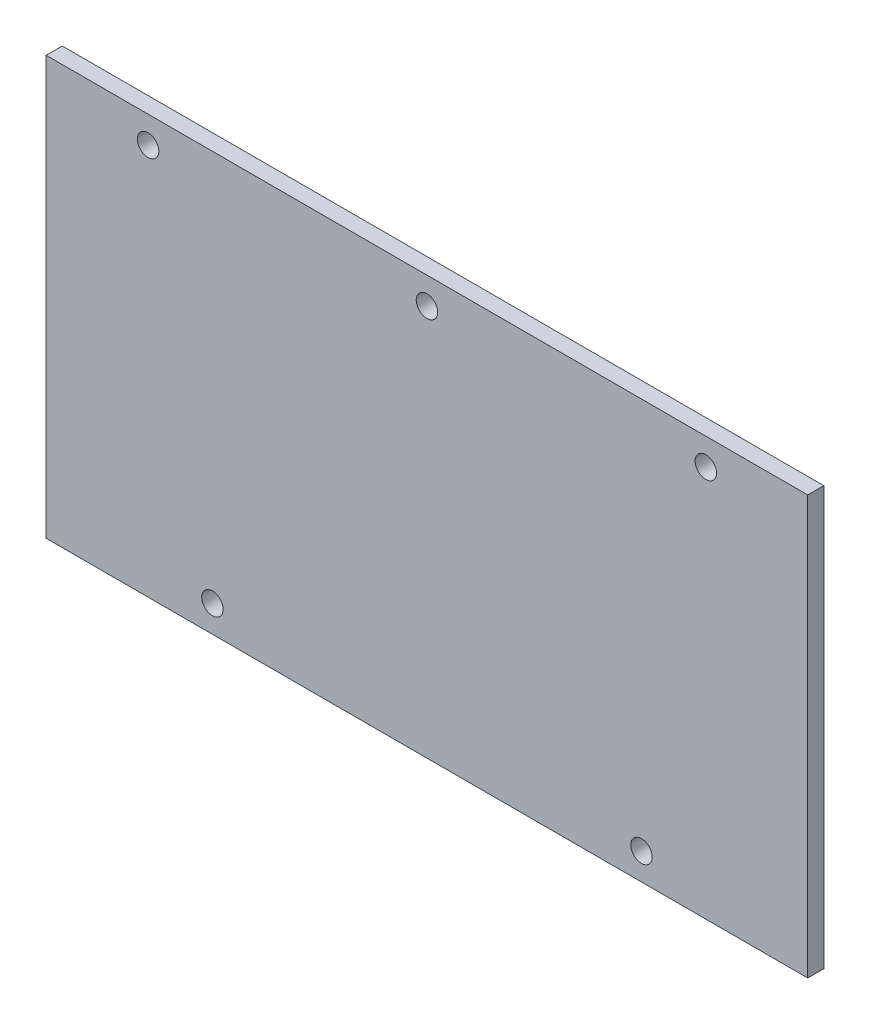
SolidWorks part; units mm, degrees
ref_plane "Спереди" through (0, 0, 0) normal (0, 0, 1) x (1, 0, 0)
ref_plane "Сверху" through (0, 0, 0) normal (0, 1, 0) x (1, 0, 0)
ref_plane "Справа" through (0, 0, 0) normal (1, 0, 0) x (0, 0, -1)
sketch "Эскиз1" plane through (0, 0, 0) normal (0, 0, 1) x (1, 0, 0)
  line L1 (35.5, 19.5) -> (-35.5, 19.5)
  line L2 (35.5, 19.5) -> (35.5, -19.5)
  line L3 (35.5, -19.5) -> (-35.5, -19.5)
  line L4 (-35.5, 19.5) -> (-35.5, -19.5)
  line L5 (35.5, 19.5) -> (-35.5, -19.5) construction
  line L6 (35.5, -19.5) -> (-35.5, 19.5) construction
  point P0 (0, 0)
  dimension "D1" = 39
  dimension "D2" = 71
extrude "Бобышка-Вытянуть1" add sketch "Эскиз1" along normal blind 1.5
sketch "Эскиз2" plane through (0, 0, 1.5) normal (0, 0, 1) x (1, 0, 0)
  line L1 (26, 17) -> (-26, 17) construction
  line L2 (26, 17) -> (26, -17) construction
  line L3 (26, -17) -> (-26, -17) construction
  line L4 (-26, 17) -> (-26, -17) construction
  line L5 (26, 17) -> (-26, -17) construction
  line L6 (26, -17) -> (-26, 17) construction
  circle A0 centre (26, 17) radius 1
  circle A1 centre (-26, 17) radius 1
  circle A2 centre (0, 17) radius 1
  circle A3 centre (20, -17) radius 1
  circle A4 centre (-20, -17) radius 1
  point P0 (0, 0)
  dimension "D3" = 2
  dimension "D4" = 2
  dimension "D5" = 2
  dimension "D7" = 2
  dimension "D9" = 2
  dimension "D1" = 34
  dimension "D2" = 52
  dimension "D6" = 20
  dimension "D8" = 20
extrude "Вырез-Вытянуть1" cut sketch "Эскиз2" against normal through all
